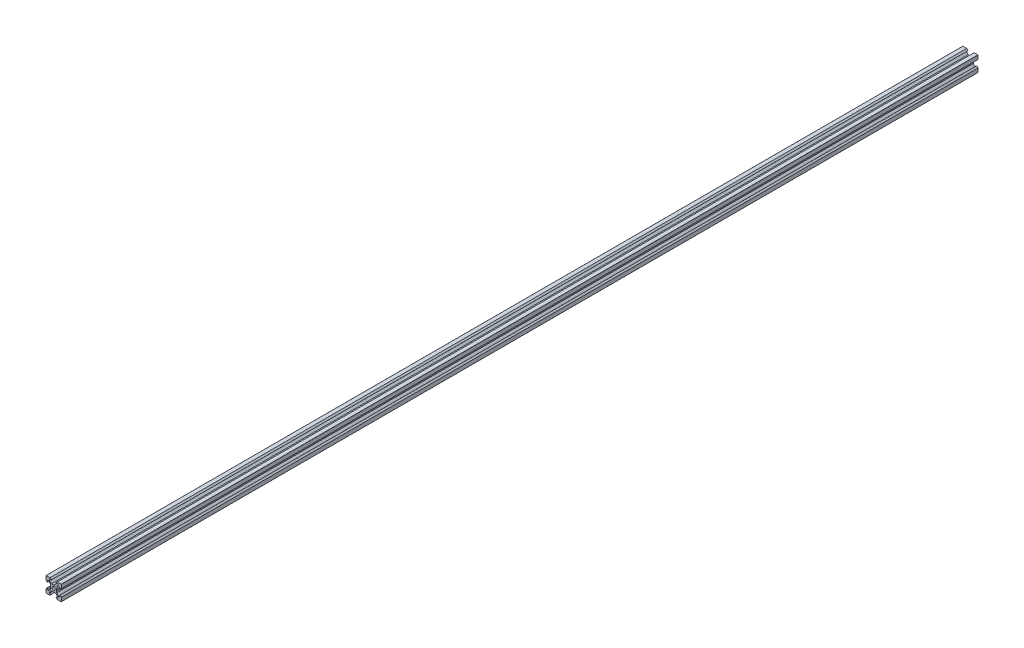
SolidWorks part; units mm, degrees
ref_plane "Front Plane" through (0, 0, 0) normal (0, 0, 1) x (1, 0, 0)
ref_plane "Top Plane" through (0, 0, 0) normal (0, 1, 0) x (1, 0, 0)
ref_plane "Right Plane" through (0, 0, 0) normal (1, 0, 0) x (0, 0, -1)
sketch "Sketch1" plane through (0, 0, 0) normal (0, 0, 1) x (1, 0, 0)
  line L0 (-11.6235, -3.5012) -> (-11.6235, -8.5612)
  line L1 (-11.4835, -8.7012) -> (-6.4235, -8.7012)
  line L2 (-6.4235, -8.7012) -> (-4.7235, -7.0012)
  line L3 (-4.7235, -7.0012) -> (-4.7235, -6.9012)
  line L4 (-4.7235, -6.9012) -> (-7.1235, -6.9012)
  line L5 (-7.1235, -6.9012) -> (-7.1235, -5.2619)
  line L6 (-7.1235, -5.2619) -> (-4.4628, -2.6012)
  line L7 (-4.4628, -2.6012) -> (-1.7735, -2.6012)
  line L8 (-1.7735, -2.6012) -> (-1.6235, -2.4512)
  line L9 (-1.6235, -2.4512) -> (-1.4735, -2.6012)
  line L10 (-1.4735, -2.6012) -> (1.2159, -2.6012)
  line L11 (1.2159, -2.6012) -> (3.8765, -5.2619)
  line L12 (3.8765, -5.2619) -> (3.8765, -6.9012)
  line L13 (3.8765, -6.9012) -> (1.4765, -6.9012)
  line L14 (1.4765, -6.9012) -> (1.4765, -7.0012)
  line L15 (1.4765, -7.0012) -> (3.1765, -8.7012)
  line L16 (3.1765, -8.7012) -> (8.2365, -8.7012)
  line L17 (8.3765, -8.5612) -> (8.3765, -3.5012)
  line L18 (8.3765, -3.5012) -> (6.6765, -1.8012)
  line L19 (6.6765, -1.8012) -> (6.5765, -1.8012)
  line L20 (6.5765, -1.8012) -> (6.5765, -4.2012)
  line L21 (6.5765, -4.2012) -> (4.9372, -4.2012)
  line L22 (4.9372, -4.2012) -> (2.2765, -1.5406)
  line L23 (2.2765, -1.5406) -> (2.2765, 1.1488)
  line L24 (2.2765, 1.1488) -> (2.1265, 1.2988)
  line L25 (2.1265, 1.2988) -> (2.2765, 1.4488)
  line L26 (2.2765, 1.4488) -> (2.2765, 4.1381)
  line L27 (2.2765, 4.1381) -> (4.9372, 6.7988)
  line L28 (4.9372, 6.7988) -> (6.5765, 6.7988)
  line L29 (6.5765, 6.7988) -> (6.5765, 4.3988)
  line L30 (6.5765, 4.3988) -> (6.6765, 4.3988)
  line L31 (6.6765, 4.3988) -> (8.3765, 6.0988)
  line L32 (8.3765, 6.0988) -> (8.3765, 11.1588)
  line L33 (8.2365, 11.2988) -> (3.1765, 11.2988)
  line L34 (3.1765, 11.2988) -> (1.4765, 9.5988)
  line L35 (1.4765, 9.5988) -> (1.4765, 9.4988)
  line L36 (1.4765, 9.4988) -> (3.8765, 9.4988)
  line L37 (3.8765, 9.4988) -> (3.8765, 7.8594)
  line L38 (3.8765, 7.8594) -> (1.2159, 5.1988)
  line L39 (1.2159, 5.1988) -> (-1.4735, 5.1988)
  line L40 (-1.4735, 5.1988) -> (-1.6235, 5.0488)
  line L41 (-1.6235, 5.0488) -> (-1.7735, 5.1988)
  line L42 (-1.7735, 5.1988) -> (-4.4628, 5.1988)
  line L43 (-4.4628, 5.1988) -> (-7.1235, 7.8594)
  line L44 (-7.1235, 7.8594) -> (-7.1235, 9.4988)
  line L45 (-7.1235, 9.4988) -> (-4.7235, 9.4988)
  line L46 (-4.7235, 9.4988) -> (-4.7235, 9.5988)
  line L47 (-4.7235, 9.5988) -> (-6.4235, 11.2988)
  line L48 (-6.4235, 11.2988) -> (-11.4835, 11.2988)
  line L49 (-11.6235, 11.1588) -> (-11.6235, 6.0988)
  line L50 (-11.6235, 6.0988) -> (-9.9235, 4.3988)
  line L51 (-9.9235, 4.3988) -> (-9.8235, 4.3988)
  line L52 (-9.8235, 4.3988) -> (-9.8235, 6.7988)
  line L53 (-9.8235, 6.7988) -> (-8.1841, 6.7988)
  line L54 (-8.1841, 6.7988) -> (-5.5235, 4.1381)
  line L55 (-5.5235, 4.1381) -> (-5.5235, 1.4488)
  line L56 (-5.5235, 1.4488) -> (-5.3735, 1.2988)
  line L57 (-5.3735, 1.2988) -> (-5.5235, 1.1488)
  line L58 (-5.5235, 1.1488) -> (-5.5235, -1.5406)
  line L59 (-5.5235, -1.5406) -> (-8.1841, -4.2012)
  line L60 (-8.1841, -4.2012) -> (-9.8235, -4.2012)
  line L61 (-9.8235, -4.2012) -> (-9.8235, -1.8012)
  line L62 (-9.8235, -1.8012) -> (-9.9235, -1.8012)
  line L63 (-9.9235, -1.8012) -> (-11.6235, -3.5012)
  arc A0 (-11.6235, -8.5612) -> (-11.4835, -8.7012) centre (-11.4835, -8.5612) ccw
  arc A1 (8.2365, -8.7012) -> (8.3765, -8.5612) centre (8.2365, -8.5612) ccw
  arc A2 (8.3765, 11.1588) -> (8.2365, 11.2988) centre (8.2365, 11.1588) ccw
  arc A3 (-11.4835, 11.2988) -> (-11.6235, 11.1588) centre (-11.4835, 11.1588) ccw
  circle A4 centre (-1.6235, 1.2988) radius 2.1
  dimension "D1" = 4.2
extrude "Boss-Extrude1" add sketch "Sketch1" along normal blind 1200
